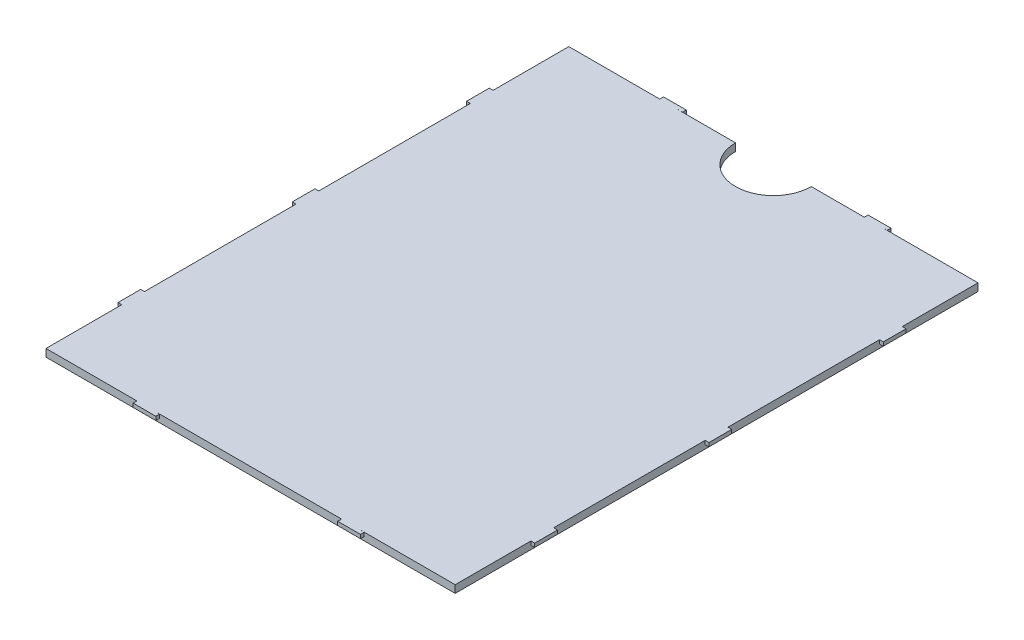
SolidWorks part; units mm, degrees
ref_plane "Front Plane" through (0, 0, 0) normal (0, 0, 1) x (1, 0, 0)
ref_plane "Top Plane" through (0, 0, 0) normal (0, 1, 0) x (1, 0, 0)
ref_plane "Right Plane" through (0, 0, 0) normal (1, 0, 0) x (0, 0, -1)
sketch "Sketch1" plane through (0, 34.2741, 0) normal (0, -1, 0) x (1, 0, 0)
  line L0 (-13.1013, 96.8075) -> (-67.1013, 96.8075) construction
  line L1 (-67.1013, 96.8075) -> (-13.1013, 96.8075)
  line L2 (-67.1013, 96.8075) -> (-67.1013, 27.8075)
  line L3 (-67.1013, 27.8075) -> (-13.1013, 27.8075)
  line L4 (-13.1013, 96.8075) -> (-13.1013, 27.8075)
extrude "Boss-Extrude1" add sketch "Sketch1" against normal blind 1
sketch "Sketch3" plane through (0, 34.2741, 0) normal (0, -1, 0) x (1, 0, 0)
  line L0 (-13.1013, 37.8075) -> (-13.1013, 40.8075)
  line L1 (-13.1013, 37.8075) -> (-12.6013, 37.8075)
  line L2 (-13.1013, 40.8075) -> (-12.6013, 40.8075)
  line L3 (-12.6013, 37.8075) -> (-12.6013, 40.8075)
  line L4 (-13.1013, 37.8075) -> (-12.6013, 40.8075) construction
  line L5 (-13.1013, 40.8075) -> (-12.6013, 37.8075) construction
  line L6 (-67.1013, 27.8075) -> (-40.1013, 27.8075)
  line L7 (-67.1013, 96.8075) -> (-13.1013, 96.8075)
  line L8 (-67.1013, 96.8075) -> (-67.1013, 27.8075)
  line L9 (-67.1013, 27.8075) -> (-13.1013, 27.8075)
  line L10 (-13.1013, 96.8075) -> (-13.1013, 27.8075)
  line L11 (-67.1013, 96.8075) -> (-13.1013, 96.8075)
  line L12 (-67.1013, 96.8075) -> (-67.1013, 27.8075)
  line L13 (-67.1013, 27.8075) -> (-13.1013, 27.8075)
  line L14 (-13.1013, 96.8075) -> (-13.1013, 27.8075)
  line L15 (-40.1013, 27.8075) -> (-13.1013, 27.8075)
  line L16 (-13.1013, 27.8075) -> (-13.1013, 50.8075)
  line L17 (-13.1013, 50.8075) -> (-13.1013, 73.8075)
  line L18 (-13.1013, 73.8075) -> (-13.1013, 96.8075)
  line L19 (-13.1013, 73.8075) -> (-13.1013, 27.8075)
  line L20 (-13.1013, 27.8075) -> (-13.1013, 50.8075) construction
  line L21 (-28.1013, 27.811) -> (-25.1013, 27.804)
  line L22 (-28.1013, 27.811) -> (-28.1024, 27.311)
  line L23 (-25.1013, 27.804) -> (-25.1024, 27.304)
  line L24 (-28.1024, 27.311) -> (-25.1024, 27.304)
  line L25 (-28.1013, 27.811) -> (-25.1024, 27.304) construction
  line L26 (-25.1013, 27.804) -> (-28.1024, 27.311) construction
  line L27 (-55.1013, 27.811) -> (-52.1013, 27.804)
  line L28 (-52.1013, 27.804) -> (-52.1024, 27.304)
  line L29 (-55.1024, 27.311) -> (-52.1024, 27.304)
  line L30 (-55.1013, 27.811) -> (-55.1024, 27.311)
  line L31 (-52.1013, 27.804) -> (-55.1024, 27.311) construction
  line L32 (-55.1013, 27.811) -> (-52.1024, 27.304) construction
  line L33 (-13.1013, 62.3075) -> (-67.1013, 62.3075) construction
  line L34 (-55.1013, 96.804) -> (-55.1024, 97.304)
  line L35 (-55.1024, 97.304) -> (-52.1024, 97.311)
  line L36 (-52.1013, 96.811) -> (-52.1024, 97.311)
  line L37 (-55.1013, 96.804) -> (-52.1013, 96.811)
  line L38 (-28.1013, 96.804) -> (-28.1024, 97.304)
  line L39 (-28.1024, 97.304) -> (-25.1024, 97.311)
  line L40 (-25.1013, 96.811) -> (-25.1024, 97.311)
  line L41 (-28.1013, 96.804) -> (-25.1013, 96.811)
  line L42 (-13.1013, 27.8075) -> (-13.1013, 39.3075)
  line L43 (-13.1013, 60.8075) -> (-13.1013, 63.8075)
  line L44 (-13.1013, 63.8075) -> (-12.6013, 63.8075)
  line L45 (-12.6013, 60.8075) -> (-12.6013, 63.8075)
  line L46 (-13.1013, 60.8075) -> (-12.6013, 60.8075)
  line L47 (-13.1013, 83.8075) -> (-13.1013, 86.8075)
  line L48 (-13.1013, 86.8075) -> (-12.6013, 86.8075)
  line L49 (-12.6013, 83.8075) -> (-12.6013, 86.8075)
  line L50 (-13.1013, 83.8075) -> (-12.6013, 83.8075)
  line L51 (-40.1013, 27.8075) -> (-40.1013, 96.8075) construction
  line L52 (-67.1013, 83.8075) -> (-67.6013, 83.8075)
  line L53 (-67.6013, 83.8075) -> (-67.6013, 86.8075)
  line L54 (-67.1013, 86.8075) -> (-67.6013, 86.8075)
  line L55 (-67.1013, 83.8075) -> (-67.1013, 86.8075)
  line L56 (-67.1013, 60.8075) -> (-67.6013, 60.8075)
  line L57 (-67.6013, 60.8075) -> (-67.6013, 63.8075)
  line L58 (-67.1013, 63.8075) -> (-67.6013, 63.8075)
  line L59 (-67.1013, 60.8075) -> (-67.1013, 63.8075)
  line L60 (-67.1013, 37.8075) -> (-67.6013, 37.8075)
  line L61 (-67.6013, 37.8075) -> (-67.6013, 40.8075)
  line L62 (-67.1013, 40.8075) -> (-67.6013, 40.8075)
  line L63 (-67.1013, 37.8075) -> (-67.1013, 40.8075)
  point P0 (-26.6018, 27.5575)
  point P2 (-12.8513, 39.3075)
  point P7 (-40.1013, 27.8075)
  point P14 (-53.6013, 27.8075)
  point P16 (-26.6013, 27.8075)
  point P21 (-13.1013, 50.8075)
  point P24 (-26.6013, 27.8075)
  point P38 (-13.1013, 39.3075)
  point P41 (-13.1013, 39.3075)
  line M4 (-13.1013, 27.8075) -> (-13.1013, 96.8075)
  dimension "D1" = 3
  dimension "D2" = 0.5
  dimension "D3" = 3
  dimension "D4" = 23
  dimension "D5" = 23
  dimension "D6" = 0.5
  dimension "D7" = 2
  dimension "D8" = 11.5
  dimension "D9" = 3
extrude "Boss-Extrude2" add sketch "Sketch3" against normal blind 0.5 from offset 0.5 contours L12 L54 L53 L52 | L18 L50 L49 L48 | L19 L46 L45 L44 | L1 L3 L2 L19 M4 | L22 L24 L23 L21 L15 | L13 L30 L29 L28 L27 | L61 L62 L63 L60 | L57 L58 L59 L56 | L35 L36 L37 L34 | L39 L40 L41 L38 offset against normal yes
sketch "Sketch4" plane through (0, 34.2741, 0) normal (0, -1, 0) x (1, 0, 0)
  line L0 (-67.1013, 27.8075) -> (-13.1013, 27.8075) construction
  circle A0 centre (-40.1013, 27.8075) radius 5
  dimension "D1" = 10
extrude "Cut-Extrude1" cut sketch "Sketch4" against normal blind 1
